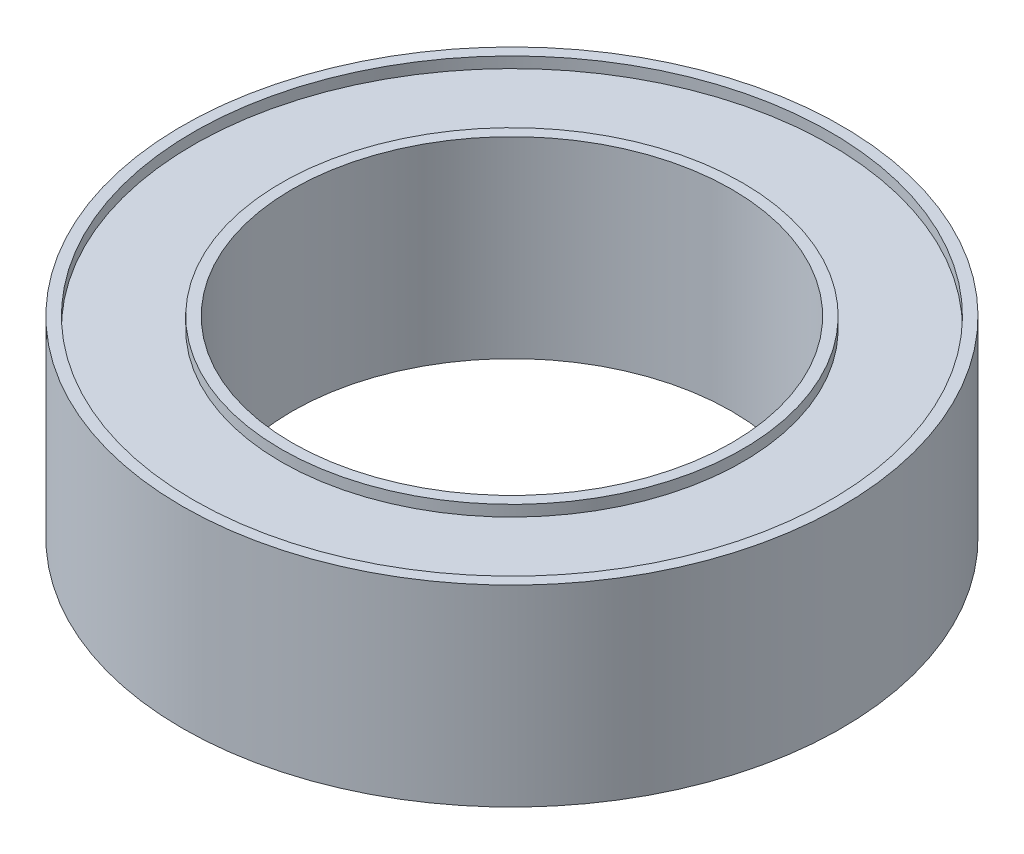
SolidWorks part; units mm, degrees
ref_plane "Front Plane" through (0, 0, 0) normal (0, 0, 1) x (1, 0, 0)
ref_plane "Top Plane" through (0, 0, 0) normal (0, 1, 0) x (1, 0, 0)
ref_plane "Right Plane" through (0, 0, 0) normal (1, 0, 0) x (0, 0, -1)
sketch "Sketch1" plane through (0, 0, 0) normal (0, 1, 0) x (1, 0, 0)
  circle A0 centre (0, 0) radius 4
  circle A1 centre (0, 0) radius 6
  dimension "D1" = 8
  dimension "D2" = 12
extrude "Boss-Extrude1" add sketch "Sketch1" along normal mid plane 3.5
sketch "Sketch2" plane through (0, 1.75, 0) normal (0, 1, 0) x (1, 0, 0)
  circle A0 centre (0, 0) radius 4.2
  circle A1 centre (0, 0) radius 5.8
  circle A2 centre (0, 0) radius 4 construction
  circle A3 centre (0, 0) radius 6 construction
  dimension "D1" = 0.2
  dimension "D2" = 0.2
extrude "Cut-Extrude1" cut sketch "Sketch2" against normal blind 0.2
mirror "Mirror2" about plane through (0, 0, 0) normal (0, 1, 0) of "Cut-Extrude1"
